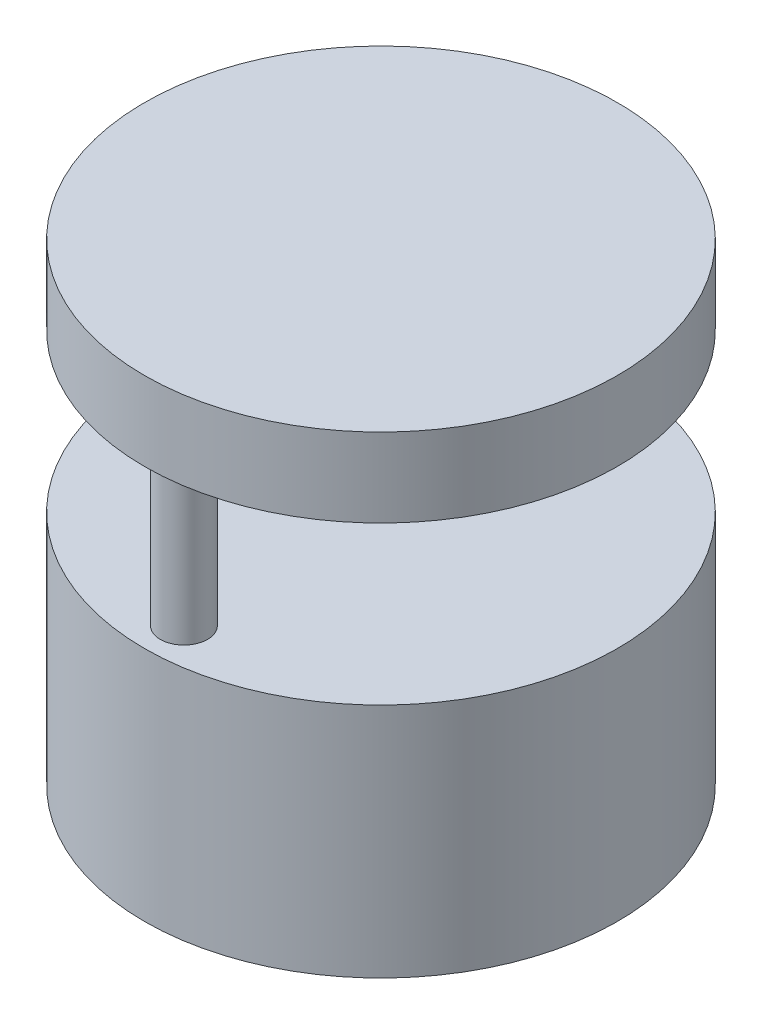
SolidWorks part; units mm, degrees
ref_plane "Front Plane" through (0, 0, 0) normal (0, 0, 1) x (1, 0, 0)
ref_plane "Top Plane" through (0, 0, 0) normal (0, 1, 0) x (1, 0, 0)
ref_plane "Right Plane" through (0, 0, 0) normal (1, 0, 0) x (0, 0, -1)
sketch "Sketch1" plane through (0, 0, 0) normal (0, 1, 0) x (1, 0, 0)
  circle A0 centre (0, 0) radius 300
extrude "Boss-Extrude1" add sketch "Sketch1" along normal blind 300
sketch "Sketch2" plane through (0, 300, 0) normal (0, 1, 0) x (1, 0, 0)
  circle A1 centre (0, 250) radius 30
  circle A2 centre (0, -250) radius 30
extrude "Boss-Extrude2" add sketch "Sketch2" along normal blind 200
ref_plane "Plane1" through (0, 500, 0) normal (0, 1, 0) x (1, 0, 0)
sketch "Sketch3" plane through (0, 500, 0) normal (0, 1, 0) x (1, 0, 0)
  circle A0 centre (0, 0) radius 300
extrude "Boss-Extrude3" add sketch "Sketch3" along normal blind 100
